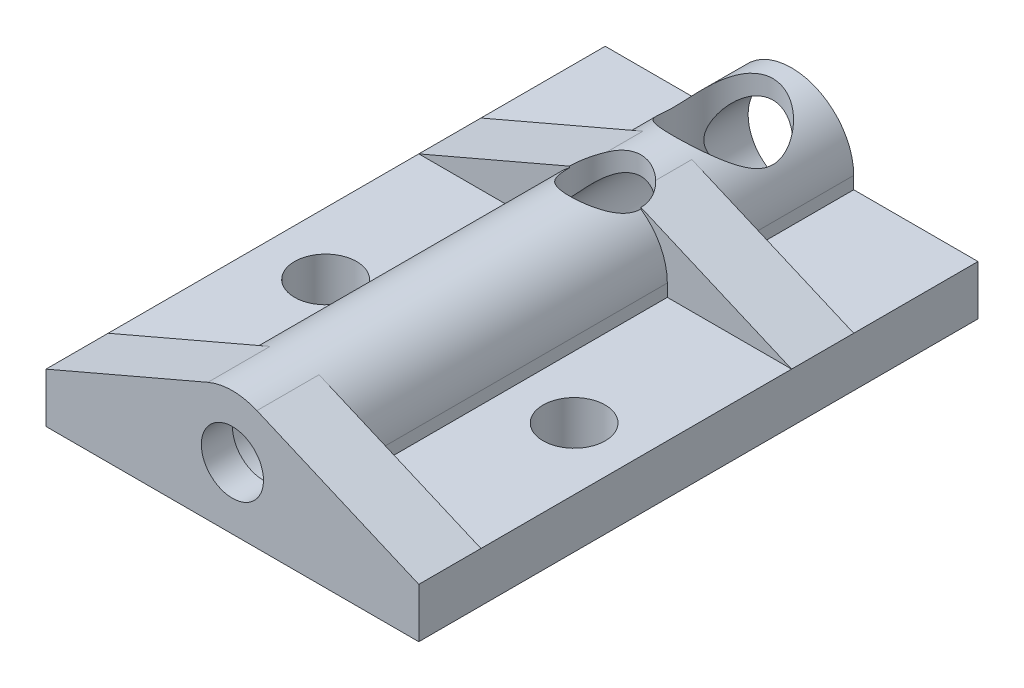
SolidWorks part; units mm, degrees
ref_plane "Front Plane" through (0, 0, 0) normal (0, 0, 1) x (1, 0, 0)
ref_plane "Top Plane" through (0, 0, 0) normal (0, 1, 0) x (1, 0, 0)
ref_plane "Right Plane" through (0, 0, 0) normal (1, 0, 0) x (0, 0, -1)
sketch "Sketch1" plane through (0, 0, 0) normal (0, 0, 1) x (1, 0, 0)
  line L1 (-5, 0) -> (-5, -5)
  line L2 (-5, -5) -> (5, -5)
  line L3 (5, -5) -> (5, 0)
  arc A1 (-5, 0) -> (5, 0) centre (0, 0) cw
  dimension "D2" = 5
  dimension "D3" = 5
extrude "Boss-Extrude1" add sketch "Sketch1" along normal blind 17.5 and the other way blind 27.5
sketch "Sketch2" plane through (0, 0, 0) normal (1, 0, 0) x (0, 0, -1)
  line L0 (27.5, -5) -> (27.5, 0) construction
  line L1 (-17.5, -5) -> (27.5, -5)
  line L2 (-17.5, -5) -> (-17.5, -1)
  line L3 (-17.5, -1) -> (27.5, -1)
  line L4 (27.5, -5) -> (27.5, -1)
  dimension "D1" = 4
extrude "Boss-Extrude2" add sketch "Sketch2" along normal blind 15 and the other way blind 15
sketch "Sketch3" plane through (0, 0, 0) normal (0, 0, 1) x (1, 0, 0)
  circle A0 centre (0, 0) radius 2.5
  dimension "D1" = 5
extrude "Cut-Extrude1" cut sketch "Sketch3" along normal through all both and the other way through all
sketch "Sketch5" plane through (0, 0, 17.5) normal (0, 0, 1) x (1, 0, 0)
  line L0 (1.973, 4.5943) -> (15, -1)
  arc A0 (5, 0) -> (-5, 0) centre (0, 0) ccw construction
rib "Rib1" sketch "Sketch5" sketch "Sketch5" thickness 5 extrusion direction parallel to sketch draft on no parameters "D1"=5
mirror "Mirror1" about plane through (0, 0, 0) normal (0, 0, 1) of "Rib1"
mirror "Mirror2" about plane through (0, 0, 0) normal (1, 0, 0) of "Mirror1", "Rib1"
sketch "Sketch7" plane through (0, 0, 0) normal (0, 1, 0) x (1, 0, 0)
  line L0 (-10, 0) -> (0, 0) construction
  line L1 (0, 0) -> (10, 0) construction
  circle A0 centre (-10, 0) radius 2.5
  circle A1 centre (10, 0) radius 2.5
  dimension "D1" = 5
  dimension "D2" = 5
  dimension "D3" = 10
  dimension "D4" = 10
extrude "Cut-Extrude2" cut sketch "Sketch7" against normal through all both
sketch "Sketch8" plane through (0, 0, 0) normal (0, 1, 0) x (1, 0, 0)
  line L0 (0, 12.5) -> (0, 0) construction
  circle A0 centre (0, 12.5) radius 2.875
  dimension "D1" = 5.75
  dimension "D2" = 12.5
extrude "Cut-Extrude3" cut sketch "Sketch8" along normal through all both and the other way through all
sketch "Sketch9" plane through (0, 0, 0) normal (0, 0, 1) x (1, 0, 0)
  circle A0 centre (0, 0) radius 3.5
  dimension "D1" = 7
extrude "Cut-Extrude4" cut sketch "Sketch9" against normal through all and the other way blind 15
sketch "Sketch10" plane through (0, 0, 0) normal (0, 1, 0) x (1, 0, 0)
  circle A0 centre (0, 22) radius 4
  dimension "D1" = 8
  dimension "D2" = 22
extrude "Cut-Extrude5" cut sketch "Sketch10" along normal through all both and the other way through all
